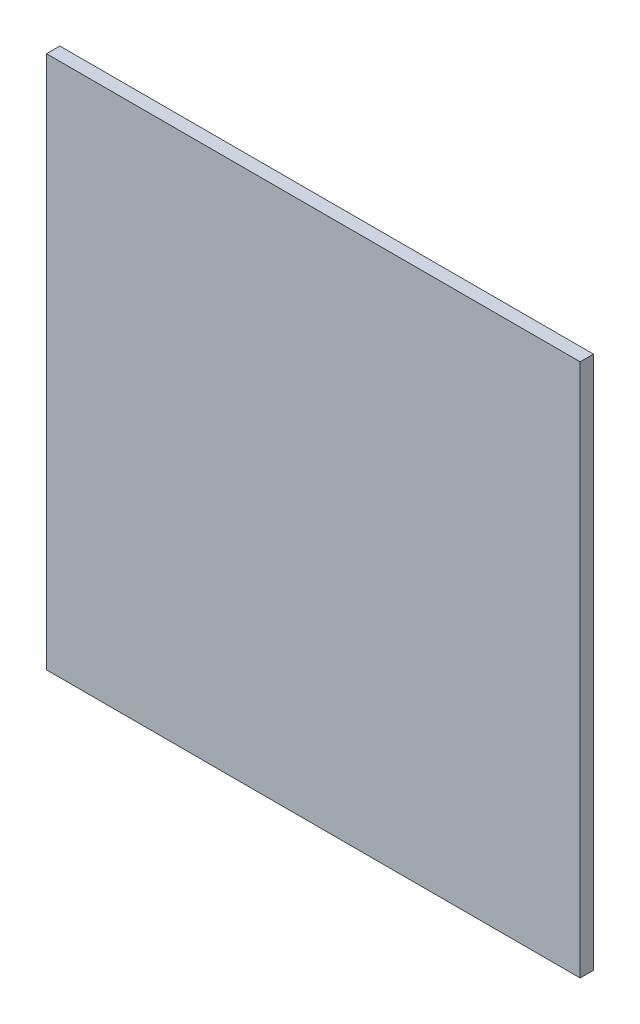
SolidWorks part; units mm, degrees
ref_plane "Front Plane" through (0, 0, 0) normal (0, 0, 1) x (1, 0, 0)
ref_plane "Top Plane" through (0, 0, 0) normal (0, 1, 0) x (1, 0, 0)
ref_plane "Right Plane" through (0, 0, 0) normal (1, 0, 0) x (0, 0, -1)
sketch "Sketch1" plane through (0, 0, 0) normal (0, 0, 1) x (1, 0, 0)
  line L1 (0, 0) -> (400, 0)
  line L2 (0, 0) -> (0, 400)
  line L3 (0, 400) -> (400, 400)
  line L4 (400, 0) -> (400, 400)
  dimension "D1" = 400
extrude "Boss-Extrude1" add sketch "Sketch1" along normal blind 10
equation "\"D1@Sketch1\" = 400"
equation "\"D1@Boss-Extrude1\"=10"
